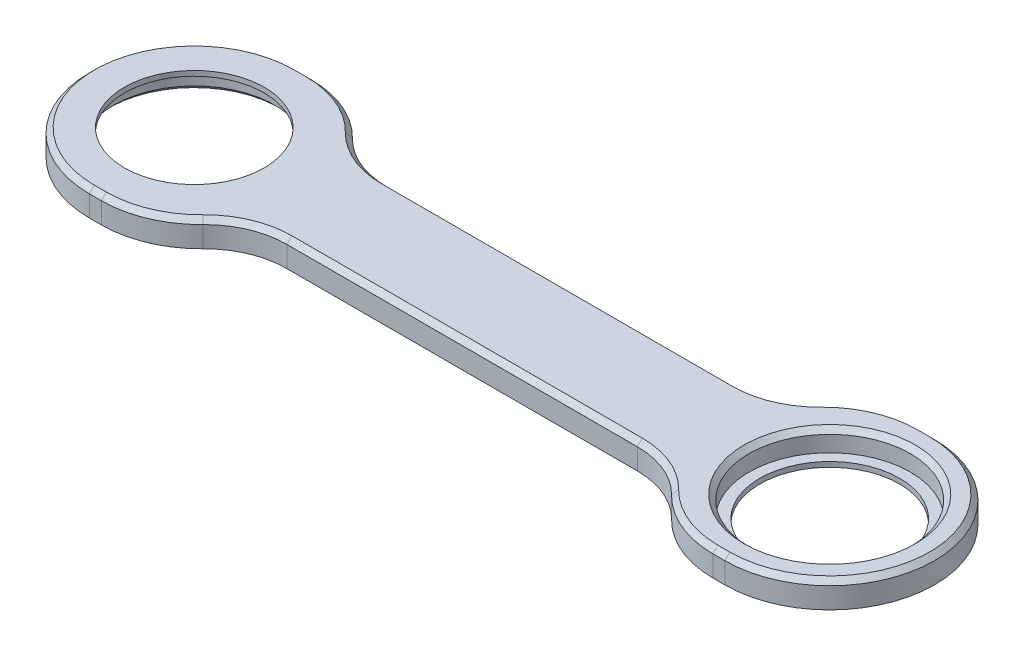
SolidWorks part; units mm, degrees
ref_plane "Front Plane" through (0, 0, 0) normal (0, 0, 1) x (1, 0, 0)
ref_plane "Top Plane" through (0, 0, 0) normal (0, 1, 0) x (1, 0, 0)
ref_plane "Right Plane" through (0, 0, 0) normal (1, 0, 0) x (0, 0, -1)
sketch "Sketch1" plane through (0, 0, 0) normal (0, 1, 0) x (1, 0, 0)
  line L0 (63.625, 0) -> (-63.625, 0) construction
  line L1 (63.625, -21) -> (-63.625, -21)
  line L2 (63.625, 21) -> (-63.625, 21)
  line L3 (-35.1066, 26.5458) -> (35.1066, 26.5458) construction
  line L4 (-35.1066, 43.0915) -> (35.1066, 43.0915)
  line L5 (-35.1066, 10) -> (35.1066, 10)
  line L6 (-35.1066, -26.5458) -> (35.1066, -26.5458) construction
  line L7 (-35.1066, -10) -> (35.1066, -10)
  line L8 (-35.1066, -43.0915) -> (35.1066, -43.0915)
  arc A0 (63.625, -21) -> (63.625, 21) centre (63.625, 0) ccw
  arc A1 (-63.625, 21) -> (-63.625, -21) centre (-63.625, 0) ccw
  circle A2 centre (-63.625, 0) radius 16.15
  arc A3 (-35.1066, 43.0915) -> (-35.1066, 10) centre (-35.1066, 26.5458) ccw
  arc A4 (35.1066, 10) -> (35.1066, 43.0915) centre (35.1066, 26.5458) ccw
  arc A5 (-35.1066, -10) -> (-35.1066, -43.0915) centre (-35.1066, -26.5458) ccw
  arc A6 (35.1066, -43.0915) -> (35.1066, -10) centre (35.1066, -26.5458) ccw
  circle A7 centre (63.625, 0) radius 16.15
  point P2 (0, 0)
  point P12 (0, 26.5458)
  point P19 (0, -26.5458)
  dimension "D2" = 32.3
  dimension "D3" = 21
  dimension "D6" = 32.3
  dimension "D1" = 127.25
  dimension "D4" = 10
  dimension "D5" = 10
extrude "Boss-Extrude1" add sketch "Sketch1" along normal blind 5.2 contours A6 L1 A0 L2 A4 L5 A3 A1 A5 L7 A7 A2
fillet "Fillet1" radius 20 4 edges at (50.6953, 2.6, 21) (50.6953, 2.6, -21) (-50.6953, 2.6, -21) (-50.6953, 2.6, 21)
chamfer "Chamfer1" distance 1 angle 45 17 edges at (63.625, 5.2, 16.15) (0, 5.2, -10) (-41.5253, 5.2, -11.2958) (41.5253, 5.2, -11.2958) (-62.433, 5.2, -21) (62.433, 5.2, -21) (-84.625, 5.2, 0) (84.625, 5.2, 0) (-62.433, 5.2, 21) (62.433, 5.2, 21) (-41.5253, 5.2, 11.2958) (41.5253, 5.2, 11.2958) (0, 5.2, 10) (-53.4822, 5.2, -19.4337) (53.4822, 5.2, -19.4337) (-53.4822, 5.2, 19.4337) (53.4822, 5.2, 19.4337)
sketch "Sketch2" plane through (0, 0, 0) normal (0, -1, 0) x (1, 0, 0)
  circle A2 centre (63.625, 0) radius 14
  circle A3 centre (63.625, 0) radius 19.0252
  dimension "D2" = 28
extrude "Boss-Extrude2" add sketch "Sketch2" against normal blind 1
sketch "Sketch3" plane through (0, 5.2, 0) normal (0, 1, 0) x (1, 0, 0)
  line L0 (77.77, 28.8659) -> (77.77, -26.5149) construction
  line L1 (0, 0) -> (86.87, 0) construction
  line L2 (79.775, 17.2779) -> (79.775, -15.919) construction
  circle A1 centre (63.625, 0) radius 16.15 construction
  dimension "D1" = 86.87
  dimension "D2" = 9.1
sketch "Sketch4" plane through (0, 5.2, 0) normal (0, 1, 0) x (1, 0, 0)
  circle A0 centre (-63.625, 0) radius 18.7153
  circle A1 centre (-63.625, 0) radius 14
  dimension "D1" = 28
extrude "Boss-Extrude3" add sketch "Sketch4" against normal blind 1
chamfer "Chamfer2" distance 1 angle 45 1 edges at (-63.625, 0, 16.15)
